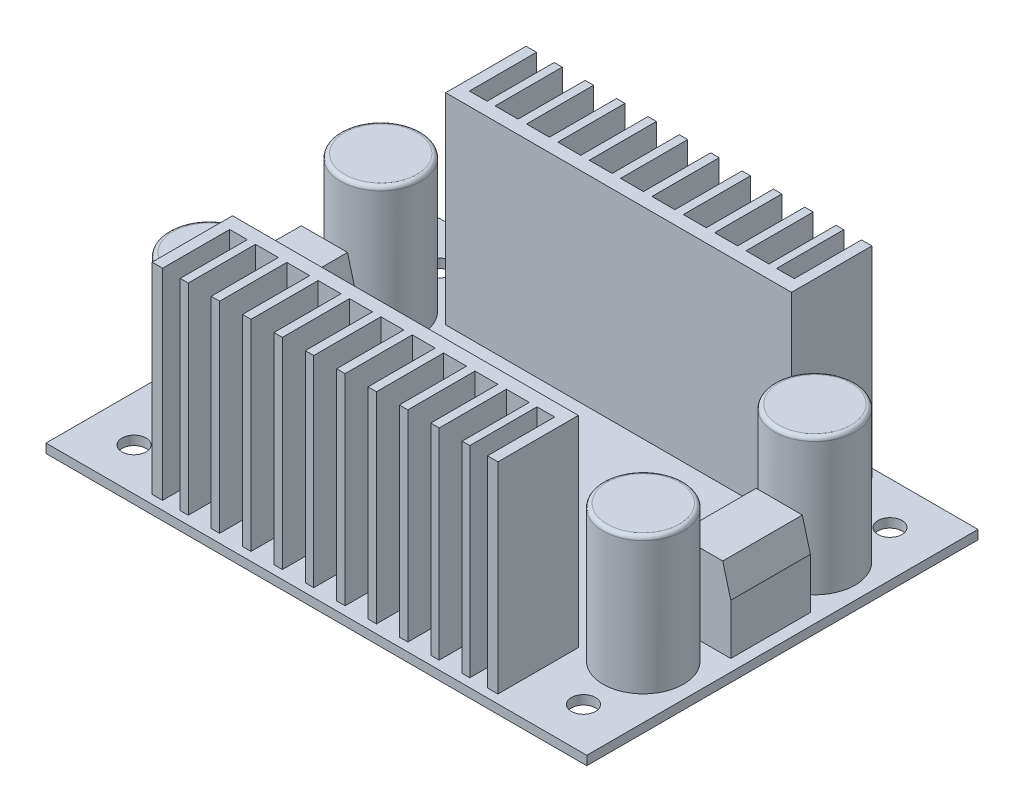
SolidWorks part; units mm, degrees
ref_plane "Front Plane" through (0, 0, 0) normal (0, 0, 1) x (1, 0, 0)
ref_plane "Top Plane" through (0, 0, 0) normal (0, 1, 0) x (1, 0, 0)
ref_plane "Right Plane" through (0, 0, 0) normal (1, 0, 0) x (0, 0, -1)
sketch "Sketch1" plane through (0, 0, 0) normal (0, 1, 0) x (1, 0, 0)
  line L1 (-33.6169, -24.3205) -> (33.6169, -24.3205)
  line L2 (-33.6169, -24.3205) -> (-33.6169, 24.3205)
  line L3 (-33.6169, 24.3205) -> (33.6169, 24.3205)
  line L4 (33.6169, -24.3205) -> (33.6169, 24.3205)
  line L5 (0, 24.3205) -> (0, -24.3205) construction
  line L6 (-33.6169, 0) -> (33.6169, 0) construction
  point P0 (0, 0)
  dimension "D1" = 48.641
  dimension "D2" = 67.2338
extrude "Boss-Extrude1" add sketch "Sketch1" along normal blind 1.1303
hole_wizard "Ø3.0mm Dowel Hole1" positions "Sketch3" profile "Sketch4" hole size "Ø3.0" standard "ANSI Metric" end condition through all
sketch "Sketch3" plane through (0, 1.1303, 0) normal (0, 1, 0) x (1, 0, 0)
  line L1 (-27.94, -19.05) -> (27.94, -19.05)
  line L2 (-27.94, -19.05) -> (-27.94, 19.05)
  line L3 (-27.94, 19.05) -> (27.94, 19.05)
  line L4 (27.94, -19.05) -> (27.94, 19.05)
  line L5 (0, 19.05) -> (0, -19.05) construction
  line L6 (-27.94, 0) -> (27.94, 0) construction
  point P454 (-27.94, 19.05)
  point P457 (27.94, 19.05)
  point P460 (27.94, -19.05)
  point P461 (-27.94, -19.05)
  point P464 (-27.94, -19.05)
  dimension "D1" = 55.88
  dimension "D2" = 38.1
sketch "Sketch4" plane through (-27.94, 1.1303, 19.05) normal (1, 0, 0) x (0, 0, 1)
  line L0 (0, 0) -> (0, 1.1303)
  line L1 (0, 1.1303) -> (1.5, 1.1303)
  line L2 (1.5, 1.1303) -> (1.5, 0)
  line L5 (1.5, 0) -> (0, 0)
  line L11 (0, -6.35) -> (0, 107.95) construction
  dimension "Thru Hole Dia." = 3
  dimension "Thru Hole Depth" = 1.1303
sketch "Sketch5" plane through (0, 1.1303, 0) normal (0, 1, 0) x (1, 0, 0)
  line L1 (26.9875, 10.668) -> (-26.9875, 10.668) construction
  line L2 (26.9875, 10.668) -> (26.9875, -10.668) construction
  line L3 (26.9875, -10.668) -> (-26.9875, -10.668) construction
  line L4 (-26.9875, 10.668) -> (-26.9875, -10.668) construction
  line L5 (0, -10.668) -> (0, 10.668) construction
  line L6 (26.9875, 0) -> (-26.9875, 0) construction
  circle A0 centre (-26.9875, 10.668) radius 5
  circle A1 centre (-26.9875, -10.668) radius 5
  circle A2 centre (26.9875, 10.668) radius 5
  circle A3 centre (26.9875, -10.668) radius 5
  point P0 (0, 0)
  point P7 (25.7654, -13.7773)
  point P9 (31.9204, -13.1332)
  dimension "D2" = 10
  dimension "D1" = 21.336
  dimension "D3" = 53.975
extrude "Boss-Extrude2" add sketch "Sketch5" along normal blind 17
fillet "Fillet1" radius 0.5 4 edges at (26.9875, 18.1303, 15.668) (26.9875, 18.1303, -5.668) (-26.9875, 18.1303, -5.668) (-26.9875, 18.1303, 15.668)
sketch "Sketch6" plane through (0, 1.1303, 0) normal (0, 1, 0) x (1, 0, 0)
  line L0 (-33.6169, 0) -> (0, 0) construction
  line L1 (-33.6169, 24.3205) -> (-33.6169, -24.3205) construction
  line L3 (-21.5, 23.25) -> (21.5, 23.25)
  line L4 (0, 0) -> (0, 24.3205) construction
  line L5 (33.6169, 24.3205) -> (-33.6169, 24.3205) construction
  line L6 (-21.5, 23.25) -> (-21.5, 13.25)
  line L7 (-21.5, 13.25) -> (21.5, 13.25)
  line L8 (21.5, 23.25) -> (21.5, 13.25)
  line L9 (0, 13.25) -> (0, 23.25) construction
  line L10 (-21.5, 18.25) -> (21.5, 18.25) construction
  point P7 (0, 12.1602)
  point P12 (0, 10.9386)
  point P250 (0, 18.25)
  dimension "D1" = 43
  dimension "D2" = 10
  dimension "D3" = 46.5
extrude "Boss-Extrude3" add sketch "Sketch6" along normal blind 25
sketch "Sketch7" plane through (0, 26.1303, 0) normal (0, 1, 0) x (1, 0, 0)
  line L0 (21.5, 23.25) -> (-21.5, 23.25) construction
  line L1 (-20.2, 23.25) -> (-18, 23.25)
  line L2 (-20.2, 23.25) -> (-20.2, 14.9)
  line L3 (-20.2, 14.9) -> (-18, 14.9)
  line L4 (-18, 23.25) -> (-18, 14.9)
  line L5 (-19.1, 14.9) -> (-19.1, 23.25) construction
  line L6 (-20.2, 19.075) -> (-18, 19.075) construction
  line L7 (-21.5, 23.25) -> (-21.5, 13.25) construction
  line L8 (-17, 23.25) -> (-14.15, 23.25)
  line L9 (-17, 23.25) -> (-17, 14.9)
  line L10 (-17, 14.9) -> (-14.15, 14.9)
  line L11 (-14.15, 23.25) -> (-14.15, 14.9)
  line L12 (-15.575, 14.9) -> (-15.575, 23.25) construction
  line L13 (-17, 19.075) -> (-14.15, 19.075) construction
  line L14 (20.2, 23.25) -> (18, 23.25)
  line L15 (20.2, 23.25) -> (20.2, 14.9)
  line L16 (20.2, 14.9) -> (18, 14.9)
  line L17 (18, 23.25) -> (18, 14.9)
  line L18 (19.1, 14.9) -> (19.1, 23.25) construction
  line L19 (20.2, 19.075) -> (18, 19.075) construction
  line L20 (21.5, 13.25) -> (21.5, 23.25) construction
  line L21 (-21.5, 13.25) -> (21.5, 13.25) construction
  line L22 (-13.1, 23.25) -> (-10.25, 23.25)
  line L23 (-13.1, 23.25) -> (-13.1, 14.9)
  line L24 (-13.1, 14.9) -> (-10.25, 14.9)
  line L25 (-10.25, 23.25) -> (-10.25, 14.9)
  line L26 (-11.675, 14.9) -> (-11.675, 23.25) construction
  line L27 (-13.1, 19.075) -> (-10.25, 19.075) construction
  line L28 (-9.2, 23.25) -> (-6.35, 23.25)
  line L29 (-9.2, 23.25) -> (-9.2, 14.9)
  line L30 (-9.2, 14.9) -> (-6.35, 14.9)
  line L31 (-6.35, 23.25) -> (-6.35, 14.9)
  line L32 (-7.775, 14.9) -> (-7.775, 23.25) construction
  line L33 (-9.2, 19.075) -> (-6.35, 19.075) construction
  line L34 (-5.3, 23.25) -> (-2.45, 23.25)
  line L35 (-5.3, 23.25) -> (-5.3, 14.9)
  line L36 (-5.3, 14.9) -> (-2.45, 14.9)
  line L37 (-2.45, 23.25) -> (-2.45, 14.9)
  line L38 (-3.875, 14.9) -> (-3.875, 23.25) construction
  line L39 (-5.3, 19.075) -> (-2.45, 19.075) construction
  line L40 (-1.4, 23.25) -> (1.45, 23.25)
  line L41 (-1.4, 23.25) -> (-1.4, 14.9)
  line L42 (-1.4, 14.9) -> (1.45, 14.9)
  line L43 (1.45, 23.25) -> (1.45, 14.9)
  line L44 (0.025, 14.9) -> (0.025, 23.25) construction
  line L45 (-1.4, 19.075) -> (1.45, 19.075) construction
  line L46 (2.5, 23.25) -> (5.35, 23.25)
  line L47 (2.5, 23.25) -> (2.5, 14.9)
  line L48 (2.5, 14.9) -> (5.35, 14.9)
  line L49 (5.35, 23.25) -> (5.35, 14.9)
  line L50 (3.925, 14.9) -> (3.925, 23.25) construction
  line L51 (2.5, 19.075) -> (5.35, 19.075) construction
  line L52 (6.4, 23.25) -> (9.25, 23.25)
  line L53 (6.4, 23.25) -> (6.4, 14.9)
  line L54 (6.4, 14.9) -> (9.25, 14.9)
  line L55 (9.25, 23.25) -> (9.25, 14.9)
  line L56 (7.825, 14.9) -> (7.825, 23.25) construction
  line L57 (6.4, 19.075) -> (9.25, 19.075) construction
  line L58 (10.3, 23.25) -> (13.15, 23.25)
  line L59 (10.3, 23.25) -> (10.3, 14.9)
  line L60 (10.3, 14.9) -> (13.15, 14.9)
  line L61 (13.15, 23.25) -> (13.15, 14.9)
  line L62 (11.725, 14.9) -> (11.725, 23.25) construction
  line L63 (10.3, 19.075) -> (13.15, 19.075) construction
  line L64 (14.2, 23.25) -> (17.05, 23.25)
  line L65 (14.2, 23.25) -> (14.2, 14.9)
  line L66 (14.2, 14.9) -> (17.05, 14.9)
  line L67 (17.05, 23.25) -> (17.05, 14.9)
  line L68 (15.625, 14.9) -> (15.625, 23.25) construction
  line L69 (14.2, 19.075) -> (17.05, 19.075) construction
  point P29 (-11.675, 19.075)
  point P37 (-7.775, 19.075)
  point P46 (-3.875, 19.075)
  point P55 (0.025, 19.075)
  point P64 (3.925, 19.075)
  point P73 (7.825, 19.075)
  point P82 (11.725, 19.075)
  point P91 (15.625, 19.075)
  point P206 (19.1, 19.075)
  point P228 (-19.1, 19.075)
  point P351 (-15.575, 19.075)
  dimension "D1" = 1.3
  dimension "D2" = 2.2
  dimension "D3" = 1.3
  dimension "D4" = 1.65
  dimension "D5" = 1
  dimension "D6" = 2.85
  dimension "D8" = 3.9
  dimension "D7" = 9
extrude "Cut-Extrude1" cut sketch "Sketch7" against normal blind 25
mirror "Mirror1" about plane through (0, 0, 0) normal (0, 0, 1) of "Cut-Extrude1", "Boss-Extrude3"
sketch "Sketch8" plane through (0, 1.1303, 0) normal (0, 1, 0) x (1, 0, 0)
  line L0 (0, 0) -> (24.4, 0) construction
  line L1 (24.4, 4.95) -> (32.15, 4.95)
  line L2 (24.4, 4.95) -> (24.4, -4.95)
  line L3 (24.4, -4.95) -> (32.15, -4.95)
  line L4 (32.15, 4.95) -> (32.15, -4.95)
  line L5 (28.275, -4.95) -> (28.275, 4.95) construction
  line L6 (24.4, 0) -> (32.15, 0) construction
  line L7 (0, 0) -> (0, 24.3205) construction
  line L8 (33.6169, 24.3205) -> (-33.6169, 24.3205) construction
  point P240 (28.275, 0)
  dimension "D1" = 9.9
  dimension "D2" = 7.75
  dimension "D3" = 64.3
extrude "Boss-Extrude4" add sketch "Sketch8" along normal blind 10
chamfer "Chamfer1" distance 1 angle 75 2 edges at (24.4, 11.1303, 0) (32.15, 11.1303, 0)
mirror "Mirror2" about plane through (0, 0, 0) normal (1, 0, 0) of "Chamfer1", "Boss-Extrude4"
